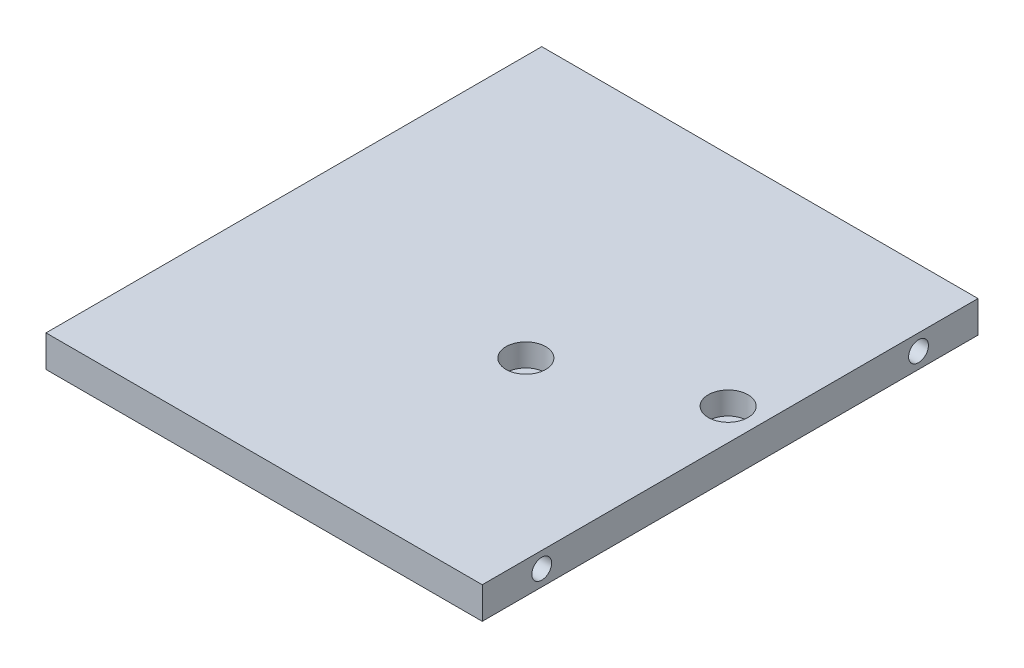
SolidWorks part; units mm, degrees
ref_plane "Front Plane" through (0, 0, 0) normal (0, 0, 1) x (1, 0, 0)
ref_plane "Top Plane" through (0, 0, 0) normal (0, 1, 0) x (1, 0, 0)
ref_plane "Right Plane" through (0, 0, 0) normal (1, 0, 0) x (0, 0, -1)
sketch "Sketch1" plane through (0, 0, 0) normal (0, 1, 0) x (1, 0, 0)
  line L1 (-55, 62.5) -> (55, 62.5)
  line L2 (-55, 62.5) -> (-55, -62.5)
  line L3 (-55, -62.5) -> (55, -62.5)
  line L4 (55, 62.5) -> (55, -62.5)
  line L5 (-55, 62.5) -> (55, -62.5) construction
  line L6 (-55, -62.5) -> (55, 62.5) construction
  point P0 (0, 0)
  dimension "D1" = 125
  dimension "D2" = 110
extrude "Boss-Extrude2" add sketch "Sketch1" along normal blind 8
sketch "Sketch2" plane through (0, 8, 0) normal (0, 1, 0) x (1, 0, 0)
  line L0 (55, 62.5) -> (-55, 62.5) construction
  line L1 (55, -62.5) -> (55, 62.5) construction
  circle A0 centre (47, 7.5) radius 2.75
  circle A1 centre (11, -7.5) radius 2.75
  dimension "D1" = 55
  dimension "D2" = 8
  dimension "D3" = 15
  dimension "D4" = 36
extrude "Cut-Extrude1" cut sketch "Sketch2" against normal blind 8
sketch "Sketch3" plane through (-55, 0, 0) normal (-1, 0, 0) x (0, 0, 1)
  line L0 (-62.5, 8) -> (-62.5, 0) construction
  line L1 (62.5, 8) -> (62.5, 0) construction
  circle A0 centre (47.5, 4) radius 2.5
  circle A1 centre (-47.5, 4) radius 2.5
  dimension "D1" = 15
  dimension "D2" = 15
extrude "Cut-Extrude2" cut sketch "Sketch3" against normal blind 15
sketch "Sketch4" plane through (55, 0, 0) normal (1, 0, 0) x (0, 0, -1)
  line L0 (-62.5, 8) -> (-62.5, 0) construction
  line L1 (62.5, 8) -> (62.5, 0) construction
  circle A0 centre (47.5, 4) radius 2.5
  circle A1 centre (-47.5, 4) radius 2.5
  dimension "D1" = 15
  dimension "D2" = 15
extrude "Cut-Extrude3" cut sketch "Sketch4" against normal blind 15
sketch "Sketch5" plane through (0, 8, 0) normal (0, 1, 0) x (1, 0, 0)
  circle A0 centre (11, -7.5) radius 5
  circle A1 centre (47, 7.5) radius 5
extrude "Cut-Extrude4" cut sketch "Sketch5" against normal blind 5.7
